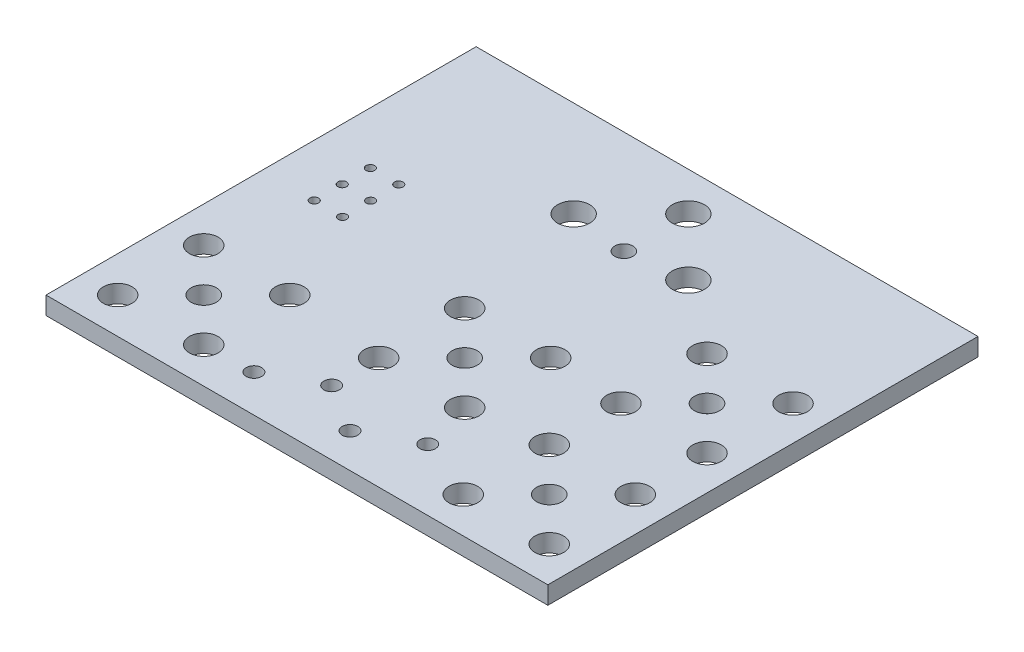
SolidWorks part; units mm, degrees
ref_plane "Front Plane" through (0, 0, 0) normal (0, 0, 1) x (1, 0, 0)
ref_plane "Top Plane" through (0, 0, 0) normal (0, 1, 0) x (1, 0, 0)
ref_plane "Right Plane" through (0, 0, 0) normal (1, 0, 0) x (0, 0, -1)
sketch "Sketch1" plane through (0, 0, 0) normal (0, 1, 0) x (1, 0, 0)
  line L1 (-22.225, 19.05) -> (22.225, 19.05)
  line L2 (-22.225, 19.05) -> (-22.225, -19.05)
  line L3 (-22.225, -19.05) -> (22.225, -19.05)
  line L4 (22.225, 19.05) -> (22.225, -19.05)
  line L5 (-22.225, 19.05) -> (22.225, -19.05) construction
  line L6 (-22.225, -19.05) -> (22.225, 19.05) construction
  circle A0 centre (-15.24, -12.065) radius 1.1176
  circle A1 centre (1.651, -16.002) radius 0.6858
  circle A2 centre (-7.112, -15.748) radius 0.6858
  circle A3 centre (-11.43, -8.255) radius 1.27
  circle A4 centre (-11.43, -15.875) radius 1.27
  circle A5 centre (-19.05, -15.875) radius 1.27
  circle A6 centre (-19.05, -8.255) radius 1.27
  circle A7 centre (15.367, -12.065) radius 1.1176
  circle A8 centre (19.177, -15.875) radius 1.27
  circle A9 centre (19.177, -8.255) radius 1.27
  circle A10 centre (11.557, -8.255) radius 1.27
  circle A11 centre (11.557, -15.875) radius 1.27
  circle A12 centre (1.143, -5.334) radius 1.1176
  circle A13 centre (4.953, -9.144) radius 1.27
  circle A14 centre (4.953, -1.524) radius 1.27
  circle A15 centre (-2.667, -1.524) radius 1.27
  circle A16 centre (-2.667, -9.144) radius 1.27
  circle A17 centre (-2.6417, -13.335) radius 0.6858
  circle A18 centre (15.367, 1.905) radius 1.1176
  circle A19 centre (11.557, -1.905) radius 1.27
  circle A20 centre (19.177, -1.905) radius 1.27
  circle A21 centre (19.177, 5.715) radius 1.27
  circle A22 centre (11.557, 5.715) radius 1.27
  circle A23 centre (6.1213, -13.589) radius 0.6858
  point P0 (0, 0)
  dimension "D3" = 2.2352
  dimension "D4" = 13.716
  dimension "D5" = 6.985
  dimension "D10" = 3.81
  dimension "D11" = 3.81
  dimension "D12" = 2.54
  dimension "D13" = 2.54
  dimension "D14" = 2.54
  dimension "D15" = 2.54
  dimension "D16" = 3.81
  dimension "D17" = 3.81
  dimension "D18" = 3.81
  dimension "D19" = 3.81
  dimension "D20" = 3.81
  dimension "D21" = 3.81
  dimension "D22" = 3.81
  dimension "D23" = 3.81
  dimension "D9" = 37.592
  dimension "D24" = 3.81
  dimension "D25" = 3.81
  dimension "D26" = 3.81
  dimension "D27" = 3.81
  dimension "D28" = 3.81
  dimension "D29" = 3.81
  dimension "D30" = 3.81
  dimension "D31" = 3.81
  dimension "D32" = 3.81
  dimension "D33" = 3.81
  dimension "D34" = 3.81
  dimension "D35" = 5.08
  dimension "D36" = 1.3716
  dimension "D37" = 1.3716
  dimension "D38" = 3.81
  dimension "D39" = 3.81
  dimension "D43" = 1.3716
  dimension "D44" = 1.3716
  dimension "D40" = 2.54
  dimension "D41" = 2.54
  dimension "D42" = 2.54
  dimension "D45" = 2.54
  dimension "D46" = 2.2352
  dimension "D47" = 13.97
  dimension "D48" = 5.08
  dimension "D49" = 8.763
  dimension "D50" = 3.81
  dimension "D51" = 3.81
  dimension "D52" = 3.81
  dimension "D53" = 3.81
  dimension "D54" = 3.81
  dimension "D55" = 3.81
  dimension "D56" = 3.81
  dimension "D57" = 3.81
  dimension "D58" = 5.715
  dimension "D59" = 4.318
  dimension "D60" = 3.302
  dimension "D61" = 3.048
  dimension "D62" = 8.763
  dimension "D1" = 38.1
  dimension "D2" = 44.45
  dimension "D6" = 6.985
  dimension "D7" = 6.985
  dimension "D8" = 23.368
extrude "Boss-Extrude1" add sketch "Sketch1" along normal blind 1.5748
sketch "Sketch2" plane through (0, 1.5748, 0) normal (0, 1, 0) x (1, 0, 0)
  line L0 (-22.225, 19.05) -> (-22.225, -19.05) construction
  line L1 (-22.225, 19.05) -> (-22.225, -19.05) construction
  line L2 (22.225, 19.05) -> (-22.225, 19.05) construction
  circle A0 centre (0, 9.906) radius 0.8001
  circle A1 centre (-17.6022, 5.0546) radius 0.381
  circle A2 centre (-17.6022, 2.5654) radius 0.381
  circle A3 centre (-17.603, 0.0833) radius 0.381
  circle A4 centre (-15.0876, 5.0546) radius 0.381
  circle A5 centre (-15.0876, 2.5654) radius 0.381
  circle A6 centre (-15.0876, 0.0762) radius 0.381
  circle A7 centre (-5.08, 10.541) radius 1.4224
  circle A8 centre (5.08, 10.541) radius 1.4224
  circle A9 centre (0, 15.621) radius 1.4224
  point P3 (-22.225, 0)
  dimension "D5" = 0.762
  dimension "D6" = 13.9954
  dimension "D9" = 0.762
  dimension "D3" = 0.762
  dimension "D10" = 0.762
  dimension "D11" = 0.762
  dimension "D12" = 0.762
  dimension "D13" = 1.6002
  dimension "D14" = 2.8448
  dimension "D15" = 2.8448
  dimension "D16" = 2.8448
  dimension "D20" = 5.08
  dimension "D22" = 3.429
  dimension "D23" = 4.6228
  dimension "D24" = 4.6228
  dimension "D2" = 4.6228
  dimension "D4" = 2.5146
  dimension "D7" = 2.4892
  dimension "D8" = 2.4892
  dimension "D17" = 0.635
  dimension "D18" = 0.635
  dimension "D19" = 5.715
  dimension "D21" = 5.08
extrude "Switch and R A connector" cut sketch "Sketch2" against normal blind 1.5748
